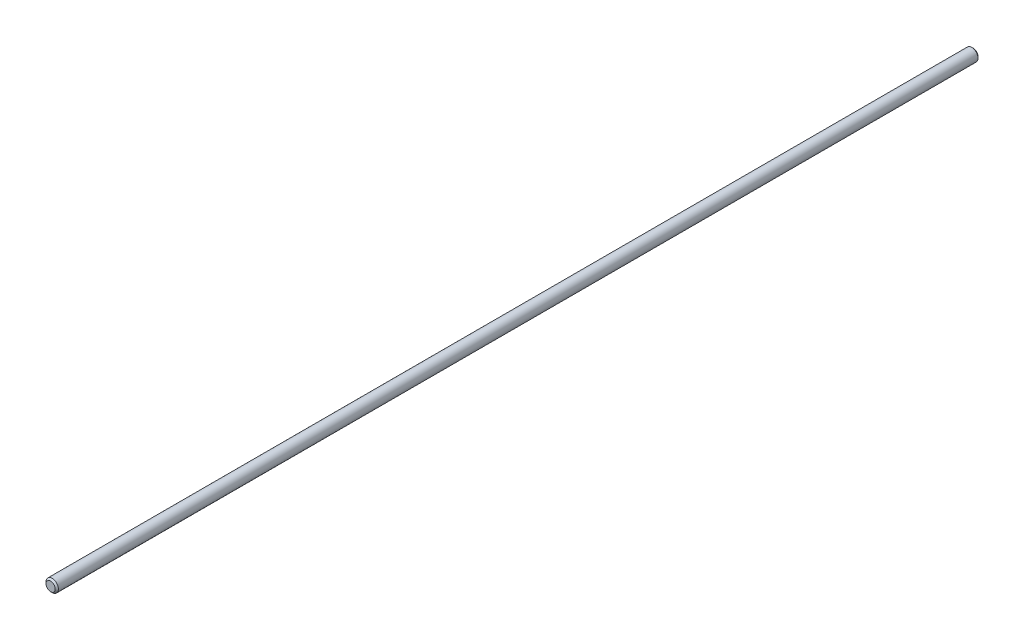
SolidWorks part; units mm, degrees
ref_plane "Front Plane" through (0, 0, 0) normal (0, 0, 1) x (1, 0, 0)
ref_plane "Top Plane" through (0, 0, 0) normal (0, 1, 0) x (1, 0, 0)
ref_plane "Right Plane" through (0, 0, 0) normal (1, 0, 0) x (0, 0, -1)
sketch "Sketch1" plane through (0, 0, 0) normal (0, 0, 1) x (1, 0, 0)
  circle A0 centre (0, 0) radius 2
  dimension "D1" = 4
extrude "Boss-Extrude1" add sketch "Sketch1" along normal blind 298.45
chamfer "Chamfer1" distance 0.508 angle 45 2 edges at (2, 0, 0) (2, 0, 298.45)
